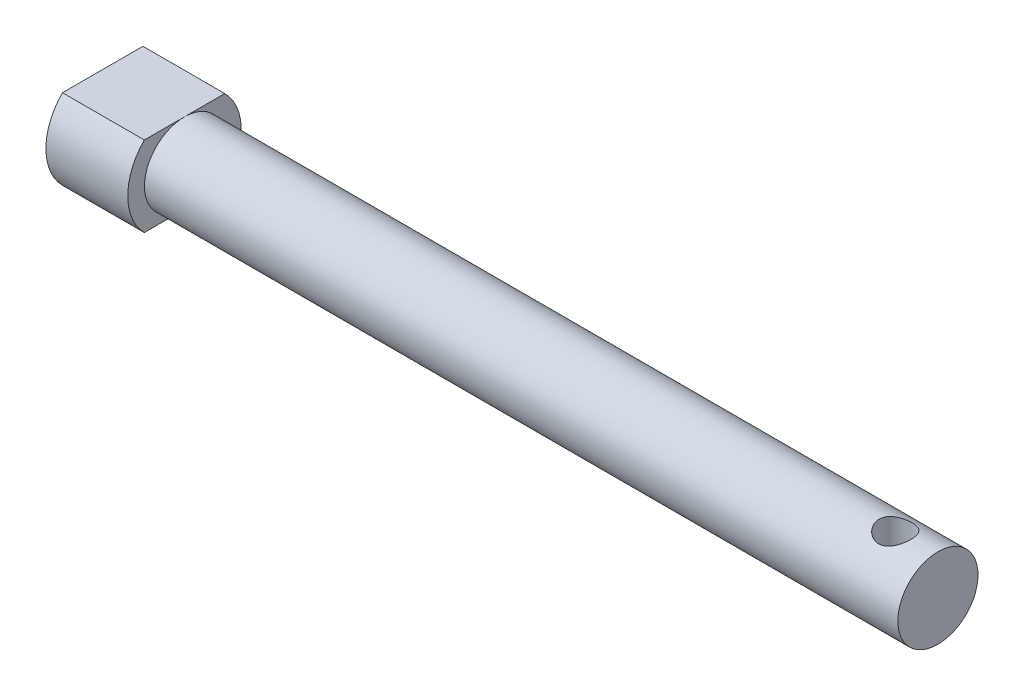
SolidWorks part; units mm, degrees
ref_plane "Front Plane" through (0, 0, 0) normal (0, 0, 1) x (1, 0, 0)
ref_plane "Top Plane" through (0, 0, 0) normal (0, 1, 0) x (1, 0, 0)
ref_plane "Right Plane" through (0, 0, 0) normal (1, 0, 0) x (0, 0, -1)
sketch "Sketch2" plane through (0, 0, 0) normal (1, 0, 0) x (0, 0, -1)
  circle A0 centre (0, 0) radius 2.4
  dimension "D1" = 4.8
extrude "Boss-Extrude1" add sketch "Sketch2" along normal mid plane 50
sketch "Sketch3" plane through (-25, 0, 0) normal (-1, 0, 0) x (0, 0, 1)
  line L0 (-2.4083, 2.4) -> (2.4083, 2.4)
  line L1 (-2.4083, -2.4) -> (2.4083, -2.4)
  circle A1 centre (0, 0) radius 2.4 construction
  circle A2 centre (0, 0) radius 3.4
  circle A3 centre (0, 0) radius 3.4
  circle M2 centre (0, 0) radius 2.4
  dimension "D1" = 1
extrude "Boss-Extrude4" add sketch "Sketch3" against normal blind 4.9 contours L1 A3 L0 M2 | L0 A3 L1 M2
sketch "Sketch5" plane through (0, 2.4, 0) normal (0, 1, 0) x (1, 0, 0)
  line L0 (-20.1, -2.4) -> (25, -2.4) construction
  line L1 (25, 2.4) -> (20.1, 2.4)
  line L2 (25, 2.4) -> (25, -2.4)
  line L3 (25, -2.4) -> (20.1, -2.4)
  line L4 (20.1, 2.4) -> (20.1, -2.4)
  circle A0 centre (22.55, -0.1) radius 1
  dimension "D2" = 2
  dimension "D1" = 4.9
  dimension "D3" = 2.45
  dimension "D4" = 2.5
extrude "Cut-Extrude2" cut sketch "Sketch5" against normal through all both and the other way through all contours A0
